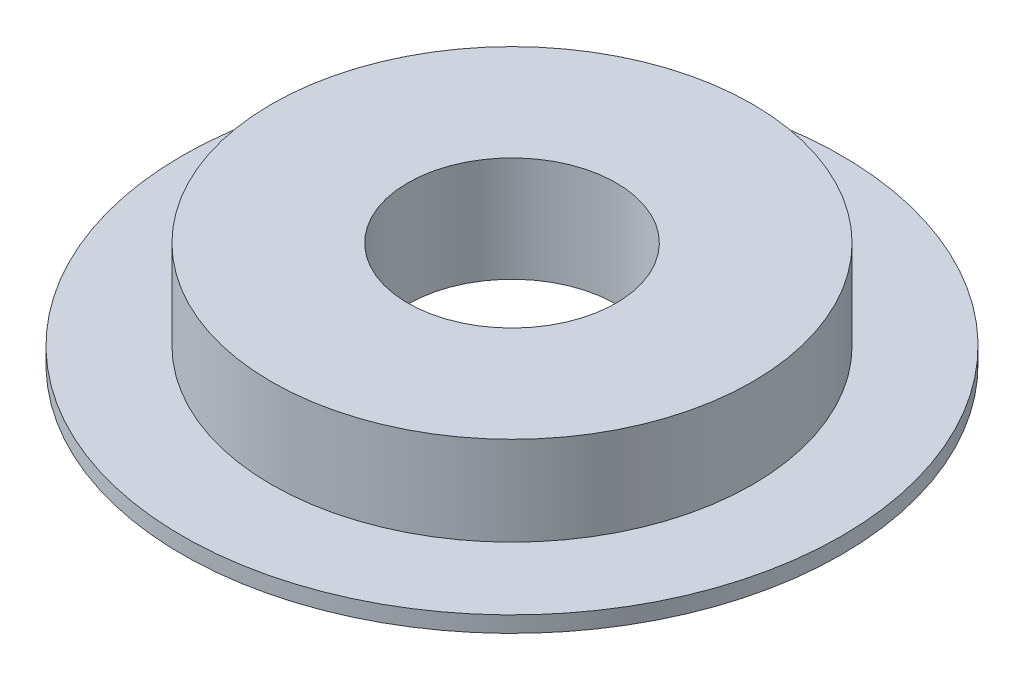
SolidWorks part; units mm, degrees
ref_plane "Alzado" through (0, 0, 0) normal (0, 0, 1) x (1, 0, 0)
ref_plane "Planta" through (0, 0, 0) normal (0, 1, 0) x (1, 0, 0)
ref_plane "Vista lateral" through (0, 0, 0) normal (1, 0, 0) x (0, 0, -1)
sketch "Croquis1" plane through (0, 0, 0) normal (0, 0, 1) x (1, 0, 0)
  line L0 (-29.0216, 13.9729) -> (-29.0216, -36.0271) construction
  line L1 (-29.0216, -11.0271) -> (-40.5216, -11.0271) construction
  line L2 (-40.7216, 8.9729) -> (-40.7216, -2.8271)
  line L3 (-29.0216, 8.9729) -> (-56.0216, 8.9729) construction
  line L4 (-40.7216, 8.9729) -> (-56.0216, 8.9729)
  line L5 (-56.0216, 8.9729) -> (-56.0216, -1.0271)
  line L6 (-56.0216, -1.0271) -> (-66.0216, -1.0271)
  line L7 (-66.0216, -1.0271) -> (-66.0216, -2.8271)
  line L8 (-66.0216, -2.8271) -> (-40.7216, -2.8271)
  dimension "D1" = 27
  dimension "D2" = 11.5
  dimension "D3" = 1.8
  dimension "D4" = 10
  dimension "D5" = 11.7
  dimension "D6" = 10
revolve "Revolución1" add sketch "Croquis1" angle 360 about L0
